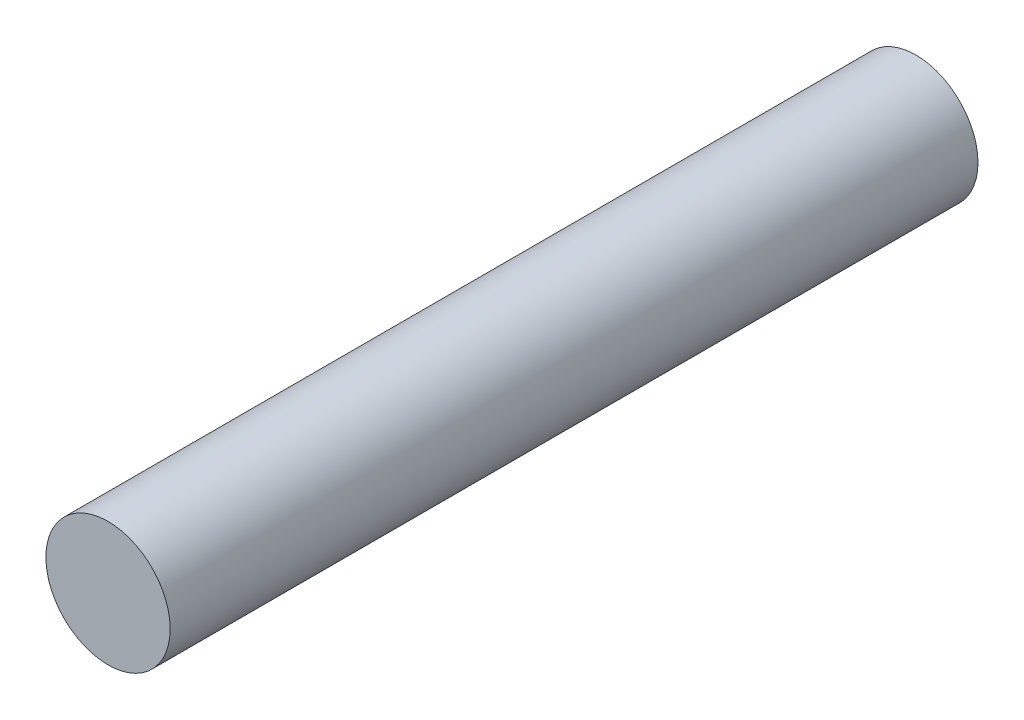
SolidWorks part; units mm, degrees
ref_plane "Front Plane" through (0, 0, 0) normal (0, 0, 1) x (1, 0, 0)
ref_plane "Top Plane" through (0, 0, 0) normal (0, 1, 0) x (1, 0, 0)
ref_plane "Right Plane" through (0, 0, 0) normal (1, 0, 0) x (0, 0, -1)
sketch "Sketch1" plane through (0, 0, 0) normal (0, 0, 1) x (1, 0, 0)
  circle A0 centre (0, 0) radius 1
  dimension "D1" = 2
extrude "Boss-Extrude1" add sketch "Sketch1" along normal blind 13
